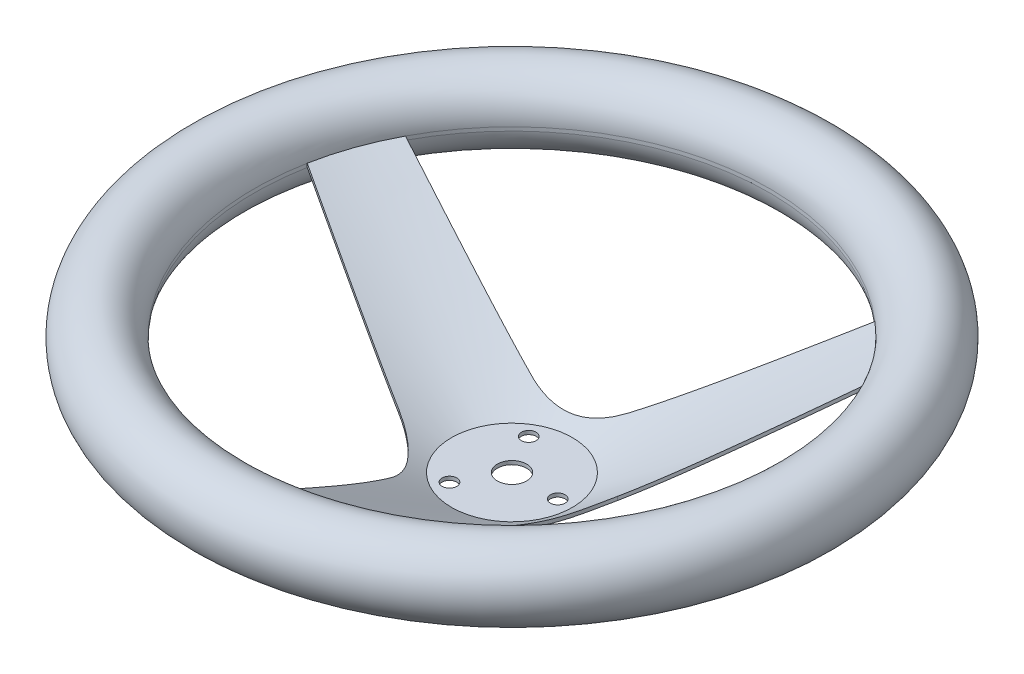
SolidWorks part; units mm, degrees
ref_plane "Front Plane" through (0, 0, 0) normal (0, 0, 1) x (1, 0, 0)
ref_plane "Top Plane" through (0, 0, 0) normal (0, 1, 0) x (1, 0, 0)
ref_plane "Right Plane" through (0, 0, 0) normal (1, 0, 0) x (0, 0, -1)
sketch "Sketch7" plane through (0, 0, 0) normal (0, 1, 0) x (1, 0, 0)
  circle A0 centre (0, 0) radius 26.162
  dimension "D1" = 52.324
extrude "Boss-Extrude4" add sketch "Sketch7" against normal blind 52.3875
sketch "Sketch8" plane through (0, 0, 0) normal (0, 1, 0) x (1, 0, 0)
  circle A0 centre (0, 0) radius 26.162
extrude "Cut-Extrude1" cut sketch "Sketch8" against normal blind 50.8
sketch "Sketch9" plane through (0, 0, 0) normal (0, 0, 1) x (1, 0, 0)
  line L0 (111.379, 0) -> (26.162, -50.8)
  line L1 (26.162, -50.8) -> (26.162, -52.3875)
  line L2 (26.162, -52.3875) -> (111.4553, -1.542)
  line L3 (0, 0) -> (0, -91.0191) construction
  circle A0 centre (127, 0) radius 15.621
  arc A1 (111.4553, -1.542) -> (111.379, 0) centre (127, 0) cw
  dimension "D2" = 31.242
  dimension "D1" = 127
revolve "Revolve4" add sketch "Sketch9" angle 360 about L3
sketch "Sketch10" plane through (0, 0, 0) normal (0, 1, 0) x (1, 0, 0)
  line L0 (94.4358, 59.0522) -> (40.5499, 5.175)
  line L1 (11.5447, 38.9355) -> (72.7286, 84.3554)
  line L2 (27.9468, -29.4657) -> (36.6896, -105.1625)
  line L7 (-98.3586, 52.2577) -> (-24.7566, 32.5298)
  line L8 (3.9227, -111.3099) -> (-15.7933, -37.7048)
  line L9 (-39.4915, -9.4697) -> (-109.4182, 20.8072)
  circle A0 centre (0, 0) radius 111.379 construction
  arc A7 (-24.7566, 32.5298) -> (11.5447, 38.9355) centre (-13.0072, 72.0088) ccw
  arc A9 (72.7286, 84.3554) -> (-98.3586, 52.2577) centre (0, 0) ccw
  arc A11 (40.5499, 5.175) -> (27.9468, -29.4657) centre (68.865, -24.7398) ccw
  arc A12 (36.6896, -105.1625) -> (94.4358, 59.0522) centre (0, 0) ccw
  arc A13 (-15.7933, -37.7048) -> (-39.4915, -9.4697) centre (-55.8578, -47.269) ccw
  arc A14 (-109.4182, 20.8072) -> (3.9227, -111.3099) centre (0, 0) ccw
  point P22 (0, 0)
  dimension "D2" = 3
  dimension "D5" = 76.2
  dimension "D11" = 76.2
extrude "Cut-Extrude2" cut sketch "Sketch10" against normal blind 50.8
sketch "Sketch11" plane through (0, -50.8, 0) normal (0, 1, 0) x (1, 0, 0)
  circle A0 centre (0, 0) radius 6.35
  circle A4 centre (19.812, 0) radius 3.175
  circle A5 centre (-9.906, 17.1577) radius 3.175
  circle A6 centre (-9.906, -17.1577) radius 3.175
extrude "Cut-Extrude3" cut sketch "Sketch11" against normal blind 2.54
